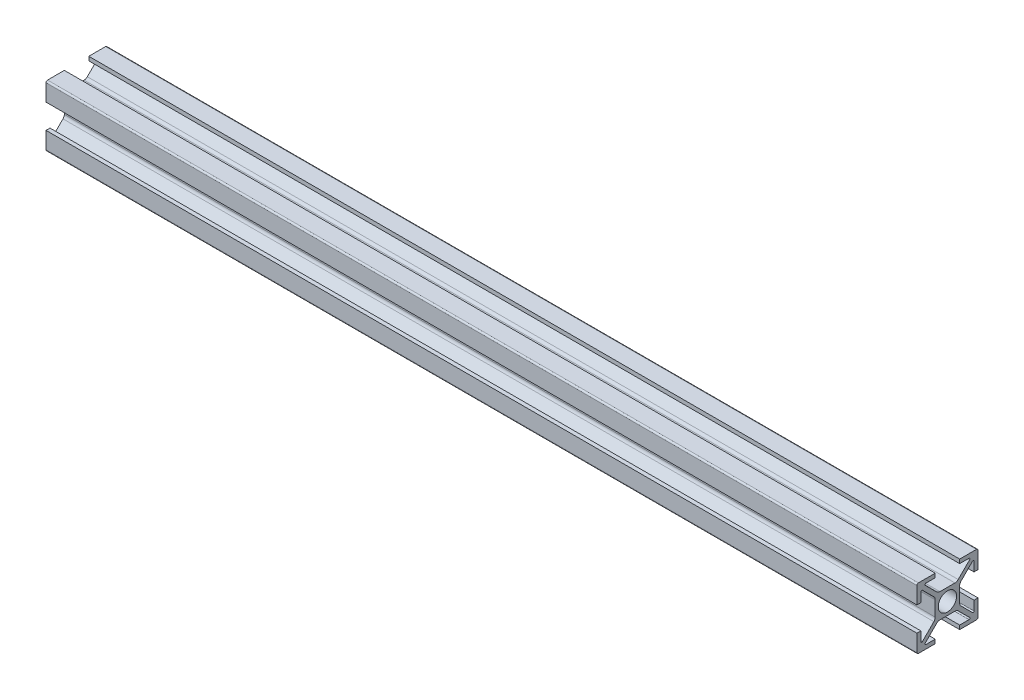
SolidWorks part; units mm, degrees
material "6061 Alloy"
ref_plane "Plano frontal" through (0, 0, 0) normal (0, 0, 1) x (1, 0, 0)
ref_plane "Plano superior" through (0, 0, 0) normal (0, 1, 0) x (1, 0, 0)
ref_plane "Plano direito" through (0, 0, 0) normal (1, 0, 0) x (0, 0, -1)
sketch "Esboço1" plane through (0, 0, 0) normal (0, 0, 1) x (1, 0, 0)
  line L0 (0, 0) -> (285, 0)
  dimension "D1" = 285
other "Quadrado PF20-01 - PERFIL 2020 BÁSICO(1)"
ref_plane "Plano1" through (0, 0, 0) normal (1, 0, 0) x (0, 1, 0)
sketch "Sketch1" plane through (0, 0, 0) normal (1, 0, 0) x (0, 1, 0)
  line L0 (8.1879, -7.2686) -> (4.4393, -3.5201)
  line L1 (4, -2.4594) -> (4, 2.4594)
  line L2 (4.4393, 3.5201) -> (8.1879, 7.2686)
  line L3 (8.7, 7.0565) -> (8.7, 4)
  line L4 (8.7, 4) -> (10, 4)
  line L5 (10, 4) -> (10, 9.5)
  line L6 (9.5, 10) -> (4, 10)
  line L7 (4, 10) -> (4, 8.7)
  line L8 (4, 8.7) -> (7.0565, 8.7)
  line L9 (7.2686, 8.1879) -> (3.5201, 4.4393)
  line L10 (2.4594, 4) -> (-2.4594, 4)
  line L11 (-3.5201, 4.4393) -> (-7.2686, 8.1879)
  line L12 (-7.0565, 8.7) -> (-4, 8.7)
  line L13 (-4, 8.7) -> (-4, 10)
  line L14 (-4, 10) -> (-9.5, 10)
  line L15 (-10, 9.5) -> (-10, 4)
  line L16 (-10, 4) -> (-8.7, 4)
  line L17 (-8.7, 4) -> (-8.7, 7.0565)
  line L18 (-8.1879, 7.2686) -> (-4.4393, 3.5201)
  line L19 (-4, 2.4594) -> (-4, -2.4594)
  line L20 (-4.4393, -3.5201) -> (-8.1879, -7.2686)
  line L21 (-8.7, -7.0565) -> (-8.7, -4)
  line L22 (-8.7, -4) -> (-10, -4)
  line L23 (-10, -4) -> (-10, -9.5)
  line L24 (-9.5, -10) -> (-4, -10)
  line L25 (-4, -10) -> (-4, -8.7)
  line L26 (-4, -8.7) -> (-7.0565, -8.7)
  line L27 (-7.2686, -8.1879) -> (-3.5201, -4.4393)
  line L28 (-2.4594, -4) -> (2.4594, -4)
  line L29 (3.5201, -4.4393) -> (7.2686, -8.1879)
  line L30 (7.0565, -8.7) -> (4, -8.7)
  line L31 (4, -8.7) -> (4, -10)
  line L32 (4, -10) -> (9.5, -10)
  line L33 (10, -9.5) -> (10, -4)
  line L34 (10, -4) -> (8.7, -4)
  line L35 (8.7, -4) -> (8.7, -7.0565)
  circle A0 centre (0, 0) radius 3
  arc A1 (8.1879, -7.2686) -> (8.7, -7.0565) centre (8.4, -7.0565) ccw
  arc A2 (4, -2.4594) -> (4.4393, -3.5201) centre (5.5, -2.4594) ccw
  arc A3 (4.4393, 3.5201) -> (4, 2.4594) centre (5.5, 2.4594) ccw
  arc A4 (8.7, 7.0565) -> (8.1879, 7.2686) centre (8.4, 7.0565) ccw
  arc A5 (10, 9.5) -> (9.5, 10) centre (9.5, 9.5) ccw
  arc A6 (7.2686, 8.1879) -> (7.0565, 8.7) centre (7.0565, 8.4) ccw
  arc A7 (2.4594, 4) -> (3.5201, 4.4393) centre (2.4594, 5.5) ccw
  arc A8 (-3.5201, 4.4393) -> (-2.4594, 4) centre (-2.4594, 5.5) ccw
  arc A9 (-7.0565, 8.7) -> (-7.2686, 8.1879) centre (-7.0565, 8.4) ccw
  arc A10 (-9.5, 10) -> (-10, 9.5) centre (-9.5, 9.5) ccw
  arc A11 (-8.1879, 7.2686) -> (-8.7, 7.0565) centre (-8.4, 7.0565) ccw
  arc A12 (-4, 2.4594) -> (-4.4393, 3.5201) centre (-5.5, 2.4594) ccw
  arc A13 (-4.4393, -3.5201) -> (-4, -2.4594) centre (-5.5, -2.4594) ccw
  arc A14 (-8.7, -7.0565) -> (-8.1879, -7.2686) centre (-8.4, -7.0565) ccw
  arc A15 (-10, -9.5) -> (-9.5, -10) centre (-9.5, -9.5) ccw
  arc A16 (-7.2686, -8.1879) -> (-7.0565, -8.7) centre (-7.0565, -8.4) ccw
  arc A17 (-2.4594, -4) -> (-3.5201, -4.4393) centre (-2.4594, -5.5) ccw
  arc A18 (3.5201, -4.4393) -> (2.4594, -4) centre (2.4594, -5.5) ccw
  arc A19 (7.0565, -8.7) -> (7.2686, -8.1879) centre (7.0565, -8.4) ccw
  arc A20 (9.5, -10) -> (10, -9.5) centre (9.5, -9.5) ccw
  point P0 (0, 10)
  point P1 (-10, 10)
  point P2 (10, 10)
  point P3 (10, 0)
  point P4 (10, -10)
  point P5 (0, -10)
  point P6 (-10, -10)
  point P7 (-10, 0)
  point P8 (0, 0)
  point P87 (0, 0)
  dimension "D2" = 20
  dimension "D3" = 5.5
  dimension "D8" = 45
  dimension "D9" = 8
  dimension "D10" = 8
